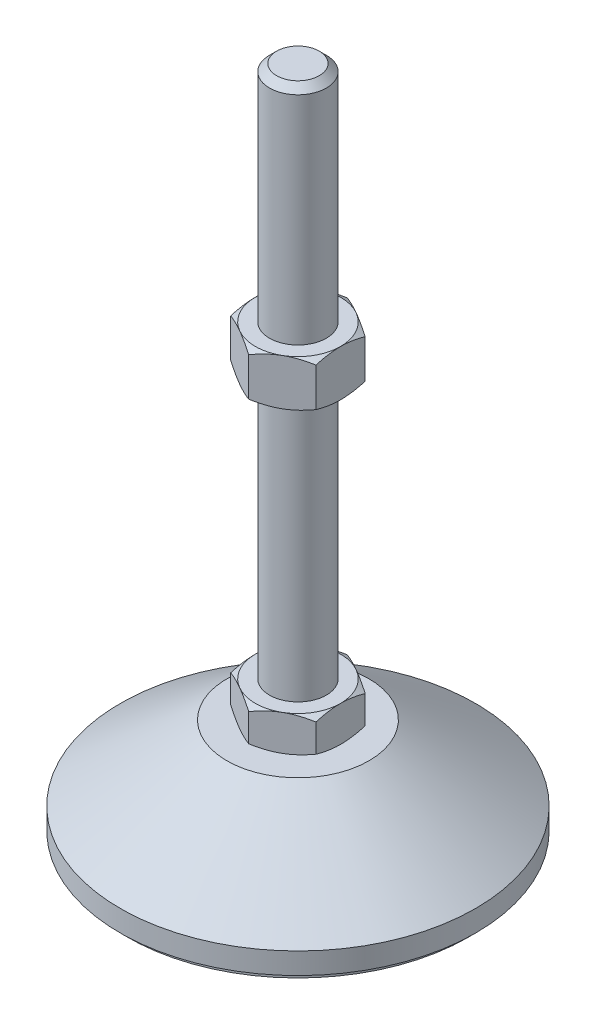
SolidWorks part; units mm, degrees
ref_plane "Спереди" through (0, 0, 0) normal (0, 0, 1) x (1, 0, 0)
ref_plane "Сверху" through (0, 0, 0) normal (0, 1, 0) x (1, 0, 0)
ref_plane "Справа" through (0, 0, 0) normal (1, 0, 0) x (0, 0, -1)
sketch "Эскиз1" plane through (0, 0, 0) normal (0, 0, 1) x (1, 0, 0)
  line L0 (0, 0) -> (-48, 0)
  line L1 (-48, 0) -> (-48, 2)
  line L2 (-48, 2) -> (-50, 2)
  line L3 (-50, 2) -> (-50, 8)
  line L4 (-50, 8) -> (-20, 29)
  line L5 (-20, 29) -> (-8, 29)
  line L12 (-8, 39) -> (-8, 187)
  line L13 (-8, 187) -> (-6, 189)
  line L14 (-6, 189) -> (0, 189)
  line L15 (0, 189) -> (0, 0) construction
  line L16 (-8, 29) -> (0, 29) construction
  line L17 (0, 0) -> (0, 189)
  line L18 (0, 0) -> (0, -7.9595) construction
  line L19 (-8, 39) -> (-8, 29)
  point P8 (-8, 113)
  point P23 (-14, 29)
  dimension "D1" = 16
  dimension "D2" = 29
  dimension "D3" = 10
  dimension "D4" = 100
  dimension "D5" = 8
  dimension "D6" = 2
  dimension "D7" = 45
  dimension "D8" = 40
  dimension "D9" = 2
  dimension "D10" = 150
  dimension "D11" = 6
revolve "Повернуть1" add sketch "Эскиз1" angle 360 about L17
sketch "Эскиз2" plane through (0, 29, 0) normal (0, 1, 0) x (1, 0, 0)
  line L1 (0, 13.8564) -> (-12, 6.9282)
  line L2 (-12, 6.9282) -> (-12, -6.9282)
  line L3 (-12, -6.9282) -> (0, -13.8564)
  line L4 (0, -13.8564) -> (12, -6.9282)
  line L5 (12, -6.9282) -> (12, 6.9282)
  line L6 (12, 6.9282) -> (0, 13.8564)
  circle A0 centre (0, 0) radius 12 construction
  dimension "D1" = 24
extrude "Бобышка-Вытянуть1" add sketch "Эскиз2" along normal up to vertex (10 mm away) up to point (-8, 39, 0)
ref_plane "Плоскость1" through (0, 113, 0) normal (0, 1, 0) x (1, 0, 0)
sketch "Эскиз3" plane through (0, 113, 0) normal (0, 1, 0) x (1, 0, 0)
  line L6 (12, 6.9282) -> (0, 13.8564)
  line L7 (0, 13.8564) -> (-12, 6.9282)
  line L8 (-12, 6.9282) -> (-12, -6.9282)
  line L9 (-12, -6.9282) -> (0, -13.8564)
  line L10 (0, -13.8564) -> (12, -6.9282)
  line L11 (12, -6.9282) -> (12, 6.9282)
  line L12 (12, 6.9282) -> (0, 13.8564)
  line L13 (0, 13.8564) -> (-12, 6.9282)
  line L14 (-12, 6.9282) -> (-12, -6.9282)
  line L15 (-12, -6.9282) -> (0, -13.8564)
  line L16 (0, -13.8564) -> (12, -6.9282)
  line L17 (12, -6.9282) -> (12, 6.9282)
  dimension "D1" = 0
extrude "Бобышка-Вытянуть2" add sketch "Эскиз3" along normal blind 13
sketch "Эскиз4" plane through (0, 0, 0) normal (0, 0, 1) x (1, 0, 0)
  line L0 (-12, 126) -> (-23.2583, 119.5)
  line L1 (-23.2583, 119.5) -> (-23.2583, 126)
  line L2 (-23.2583, 126) -> (-12, 126)
  line L3 (-23.2583, 119.5) -> (-12, 113)
  line L4 (50, 113) -> (-50, 113) construction
  line L5 (-12, 113) -> (-23.2583, 113)
  line L6 (-23.2583, 113) -> (-23.2583, 119.5)
  line L7 (-12, 126) -> (-12, 113) construction
  line L8 (-12, 39) -> (-20.6603, 39)
  line L9 (-20.6603, 39) -> (-20.6603, 34)
  line L10 (-20.6603, 34) -> (-12, 39)
  line L11 (-12, 29) -> (-20.6603, 34)
  line L12 (-20.6603, 34) -> (-20.6603, 29)
  line L13 (-20.6603, 29) -> (-12, 29)
  line L14 (0, 189) -> (0, 96.3793) construction
  dimension "D1" = 30
  dimension "D2" = 30
revolve "Вырез-Повернуть2" cut sketch "Эскиз4" angle 360 about L14
